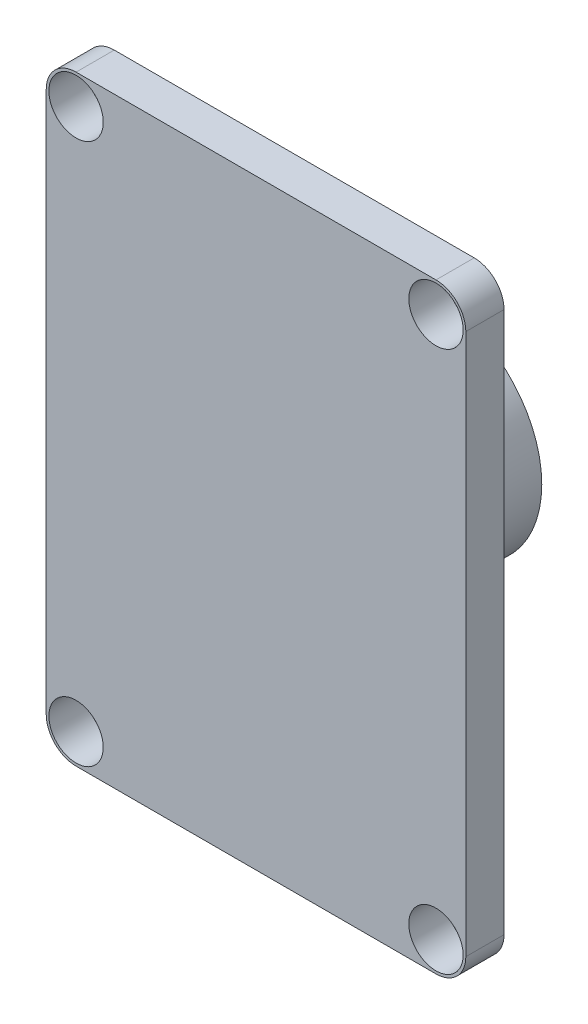
SolidWorks part; units mm, degrees
ref_plane "Front Plane" through (0, 0, 0) normal (0, 0, 1) x (1, 0, 0)
ref_plane "Top Plane" through (0, 0, 0) normal (0, 1, 0) x (1, 0, 0)
ref_plane "Right Plane" through (0, 0, 0) normal (1, 0, 0) x (0, 0, -1)
sketch "Sketch2" plane through (0, 0, 0) normal (0, 0, 1) x (1, 0, 0)
  line L0 (0, 0) -> (0, 25.9114) construction
  line L1 (-7.6581, -12.7889) -> (7.6581, -12.7889)
  line L2 (-8.9281, -11.5189) -> (-8.9281, 11.5189)
  line L3 (-7.6581, 12.7889) -> (7.6581, 12.7889)
  line L4 (8.9281, -11.5189) -> (8.9281, 11.5189)
  line L5 (-8.9281, -12.7889) -> (8.9281, 12.7889) construction
  line L6 (-8.9281, 12.7889) -> (8.9281, -12.7889) construction
  line L7 (0, 25.9114) -> (0, 0) construction
  line L8 (0, 0) -> (-11.5478, 0) construction
  arc A0 (-7.6581, -12.7889) -> (-8.9281, -11.5189) centre (-7.6581, -11.5189) cw
  arc A1 (8.9281, -11.5189) -> (7.6581, -12.7889) centre (7.6581, -11.5189) cw
  arc A2 (8.9281, 11.5189) -> (7.6581, 12.7889) centre (7.6581, 11.5189) ccw
  arc A3 (-7.6581, 12.7889) -> (-8.9281, 11.5189) centre (-7.6581, 11.5189) ccw
  circle A4 centre (7.6581, 11.5189) radius 1.1564
  circle A5 centre (-7.6581, 11.5189) radius 1.1564
  circle A6 centre (7.6581, -11.5189) radius 1.1564
  circle A7 centre (-7.6581, -11.5189) radius 1.1564
  point P0 (0, 0)
  dimension "D3" = 1.27
  dimension "D1" = 25.5778
  dimension "D2" = 17.8562
extrude "Boss-Extrude1" add sketch "Sketch2" along normal blind 1.6256
sketch "Sketch3" plane through (0, 0, 0) normal (0, 0, -1) x (-1, 0, 0)
  circle A0 centre (0, 0) radius 4.6545
  dimension "D1" = 9.3091
extrude "Boss-Extrude2" add sketch "Sketch3" along normal blind 5.8801
